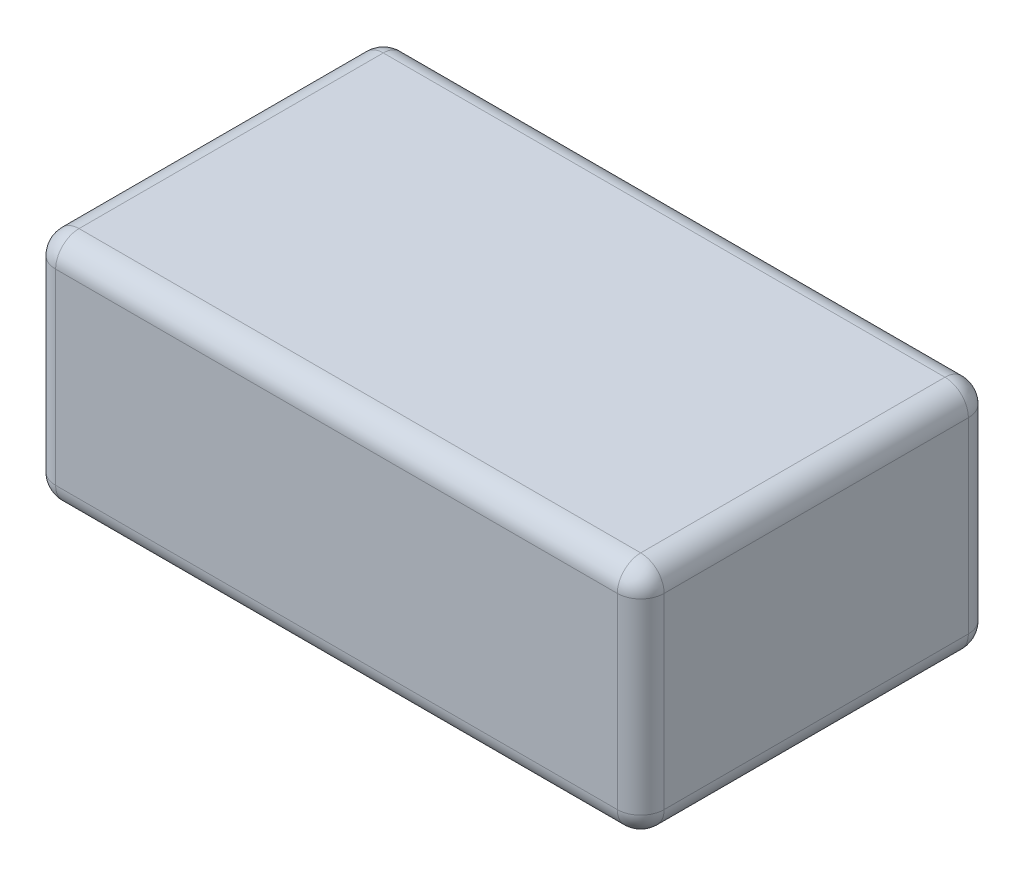
SolidWorks part; units mm, degrees
ref_plane "Front Plane" through (0, 0, 0) normal (0, 0, 1) x (1, 0, 0)
ref_plane "Top Plane" through (0, 0, 0) normal (0, 1, 0) x (1, 0, 0)
ref_plane "Right Plane" through (0, 0, 0) normal (1, 0, 0) x (0, 0, -1)
sketch "Sketch1" plane through (0, 0, 0) normal (0, 1, 0) x (1, 0, 0)
  line L1 (-26, -15) -> (26, -15)
  line L2 (-26, -15) -> (-26, 15)
  line L3 (-26, 15) -> (26, 15)
  line L4 (26, -15) -> (26, 15)
  line L5 (-26, -15) -> (26, 15) construction
  line L6 (-26, 15) -> (26, -15) construction
  point P0 (0, 0)
  dimension "D1" = 52
  dimension "D2" = 30
extrude "Boss-Extrude1" add sketch "Sketch1" along normal blind 20
fillet "Fillet1" radius 2 12 edges at (26, 0, 0) (0, 0, 15) (26, 20, 0) (0, 20, -15) (-26, 20, 0) (0, 20, 15) (26, 10, 15) (-26, 10, 15) (26, 10, -15) (0, 0, -15) (-26, 10, -15) (-26, 0, 0)
